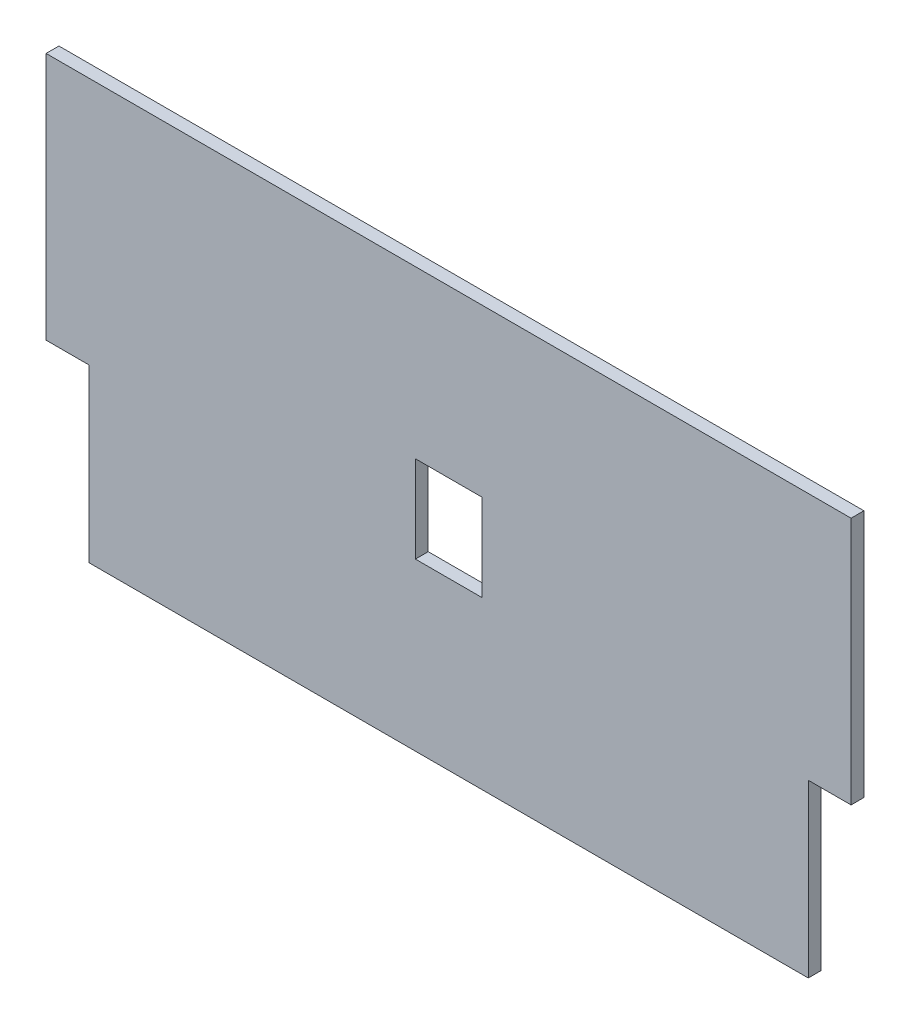
SolidWorks part; units mm, degrees
ref_plane "Plano frontal" through (0, 0, 0) normal (0, 0, 1) x (1, 0, 0)
ref_plane "Plano superior" through (0, 0, 0) normal (0, 1, 0) x (1, 0, 0)
ref_plane "Plano direito" through (0, 0, 0) normal (1, 0, 0) x (0, 0, -1)
sketch "Esboço1" plane through (0, 0, 0) normal (0, 0, 1) x (1, 0, 0)
  line L0 (-94, 0) -> (94, 0)
  line L1 (94, 0) -> (94, -58)
  line L2 (94, -58) -> (84, -58)
  line L3 (84, -58) -> (84, -98)
  line L4 (84, -98) -> (-84, -98)
  line L5 (0, 0) -> (0, -98) construction
  line L6 (-84, -58) -> (-84, -98)
  line L7 (-94, -58) -> (-84, -58)
  line L8 (-94, 0) -> (-94, -58)
  dimension "D1" = 98
  dimension "D2" = 10
  dimension "D3" = 40
  dimension "D4" = 94
extrude "Ressalto-extrusão1" add sketch "Esboço1" along normal mid plane 3
sketch "Esboço2" plane through (0, 0, 1.5) normal (0, 0, 1) x (1, 0, 0)
  line L0 (0, 0) -> (0, -98) construction
  line L1 (94, 0) -> (-94, 0) construction
  line L2 (-84, -98) -> (84, -98) construction
  line L3 (0, -49) -> (-94, -49) construction
  line L4 (-94, 0) -> (-94, -58) construction
  line L6 (-7.75, -38.85) -> (7.75, -38.85)
  line L7 (-7.75, -38.85) -> (-7.75, -59.15)
  line L8 (-7.75, -59.15) -> (7.75, -59.15)
  line L9 (7.75, -38.85) -> (7.75, -59.15)
  line L10 (-7.75, -38.85) -> (7.75, -59.15) construction
  line L11 (-7.75, -59.15) -> (7.75, -38.85) construction
  dimension "D1" = 20.3
  dimension "D2" = 15.5
extrude "Corte-extrusão1" cut sketch "Esboço2" against normal blind 3
